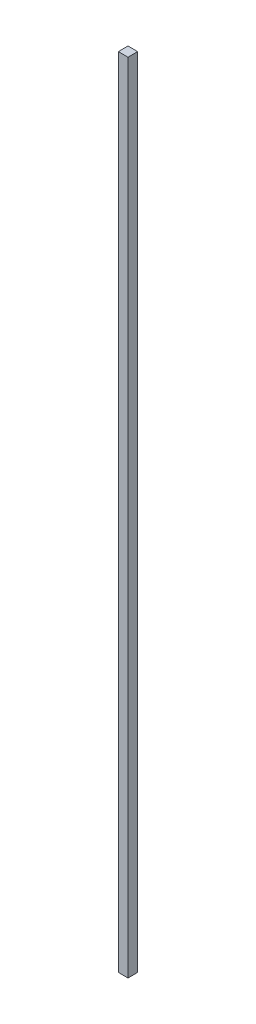
SolidWorks part; units mm, degrees
ref_plane "Front Plane" through (0, 0, 0) normal (0, 0, 1) x (1, 0, 0)
ref_plane "Top Plane" through (0, 0, 0) normal (0, 1, 0) x (1, 0, 0)
ref_plane "Right Plane" through (0, 0, 0) normal (1, 0, 0) x (0, 0, -1)
sketch "Sketch1" plane through (0, 0, 0) normal (1, 0, 0) x (0, 0, -1)
  line L0 (0, 0) -> (0, 2470)
  line L1 (0, 2470) -> (30, 2470)
  line L2 (30, 2470) -> (30, 0)
  line L3 (30, 0) -> (0, 0)
  dimension "D1" = 30
  dimension "D2" = 2470
extrude "Boss-Extrude1" add sketch "Sketch1" along normal mid plane 30
sketch "Sketch2" plane through (0, 0, 0) normal (0, -1, 0) x (1, 0, 0)
  line L0 (15, 0) -> (-15, 0) construction
  circle A0 centre (0, -15) radius 2.5
  dimension "D1" = 5
  dimension "D2" = 15
extrude "Boss-Extrude2" add sketch "Sketch2" along normal blind 10
